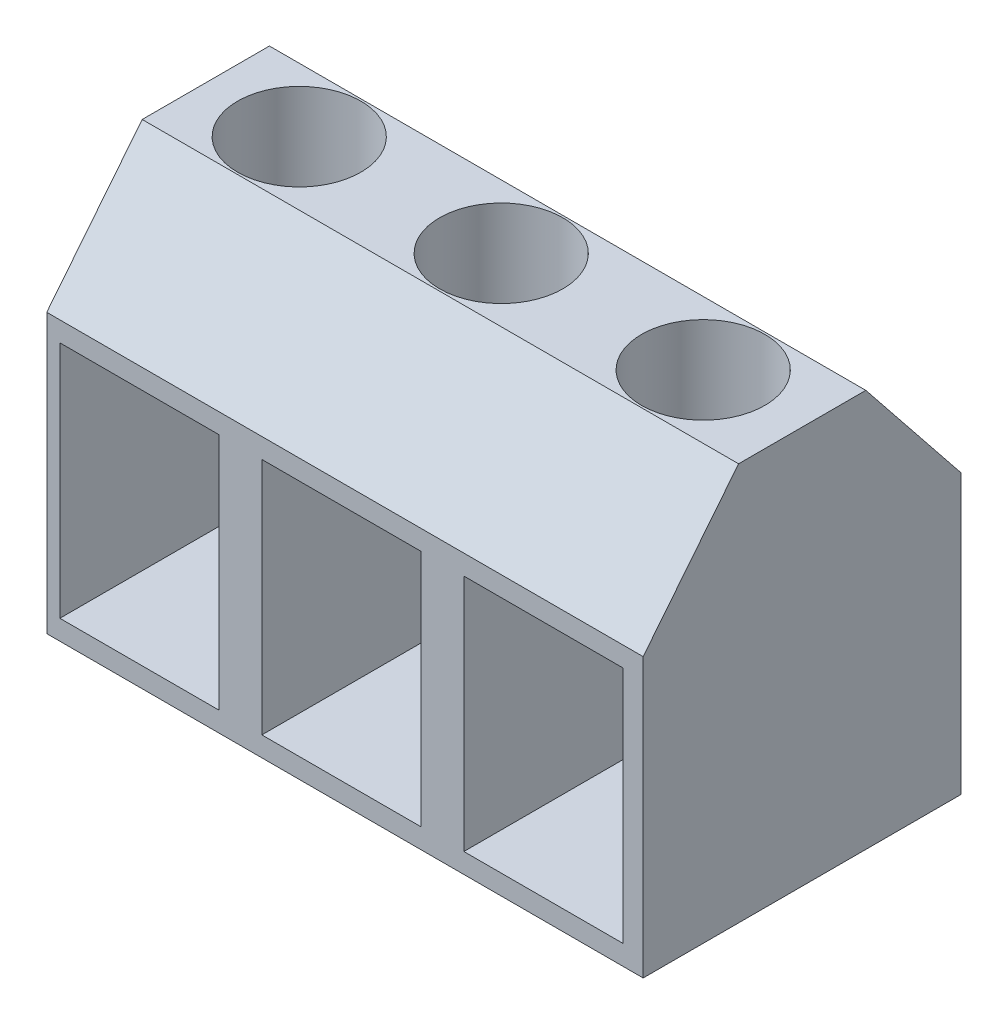
SolidWorks part; units mm, degrees
material "ABS"
ref_plane "Front Plane" through (0, 0, 0) normal (0, 0, 1) x (1, 0, 0)
ref_plane "Top Plane" through (0, 0, 0) normal (0, 1, 0) x (1, 0, 0)
ref_plane "Right Plane" through (0, 0, 0) normal (1, 0, 0) x (0, 0, -1)
sketch "Sketch1" plane through (0, 0, 0) normal (1, 0, 0) x (0, 0, -1)
  line L0 (-0.451, -0.7669) -> (2.749, -0.7669)
  line L1 (2.749, -0.7669) -> (5.149, -3.7669)
  line L2 (5.149, -3.7669) -> (5.149, -10.7669)
  line L3 (5.149, -10.7669) -> (-2.851, -10.7669)
  line L4 (-2.851, -10.7669) -> (-2.851, -3.7669)
  line L5 (-2.851, -3.7669) -> (-0.451, -0.7669)
  dimension "D1" = 3.2
  dimension "D2" = 8
  dimension "D3" = 10
  dimension "D4" = 7
extrude "Boss-Extrude1" add sketch "Sketch1" along normal blind 15
sketch "Sketch2" plane through (0, 0, 2.851) normal (0, 0, 1) x (1, 0, 0)
  line L0 (0, -3.7669) -> (0, -10.7669) construction
  line L1 (0.33, -10.2669) -> (4.33, -10.2669)
  line L2 (0.33, -10.2669) -> (0.33, -4.2669)
  line L3 (0.33, -4.2669) -> (4.33, -4.2669)
  line L4 (4.33, -10.2669) -> (4.33, -4.2669)
  line L5 (15, -10.7669) -> (0, -10.7669) construction
  line L6 (5.41, -10.2669) -> (9.41, -10.2669)
  line L7 (5.41, -10.2669) -> (5.41, -4.2669)
  line L8 (5.41, -4.2669) -> (9.41, -4.2669)
  line L9 (9.41, -10.2669) -> (9.41, -4.2669)
  line L10 (10.49, -10.2669) -> (14.49, -10.2669)
  line L11 (10.49, -10.2669) -> (10.49, -4.2669)
  line L12 (10.49, -4.2669) -> (14.49, -4.2669)
  line L13 (14.49, -10.2669) -> (14.49, -4.2669)
  dimension "D1" = 0.33
  dimension "D2" = 0.5
  dimension "D3" = 6
  dimension "D4" = 4
  dimension "D5" = 3
extrude "Cut-Extrude1" cut sketch "Sketch2" against normal offset from surface (7.5 mm away) 0.5 up to face at (7.5, -7.2669, -5.149)
sketch "Sketch3" plane through (0, -0.7669, 0) normal (0, 1, 0) x (1, 0, 0)
  line L0 (0, 2.749) -> (0, -0.451) construction
  circle A0 centre (2.35, 1.149) radius 1.55
  circle A1 centre (7.43, 1.149) radius 1.55
  circle A2 centre (12.51, 1.149) radius 1.55
  dimension "D1" = 2.35
  dimension "D3" = 3.1
  dimension "D2" = 3
extrude "Cut-Extrude2" cut sketch "Sketch3" against normal up to surface (3.5 mm away) up to face at (2.33, -4.2669, -0.899)
